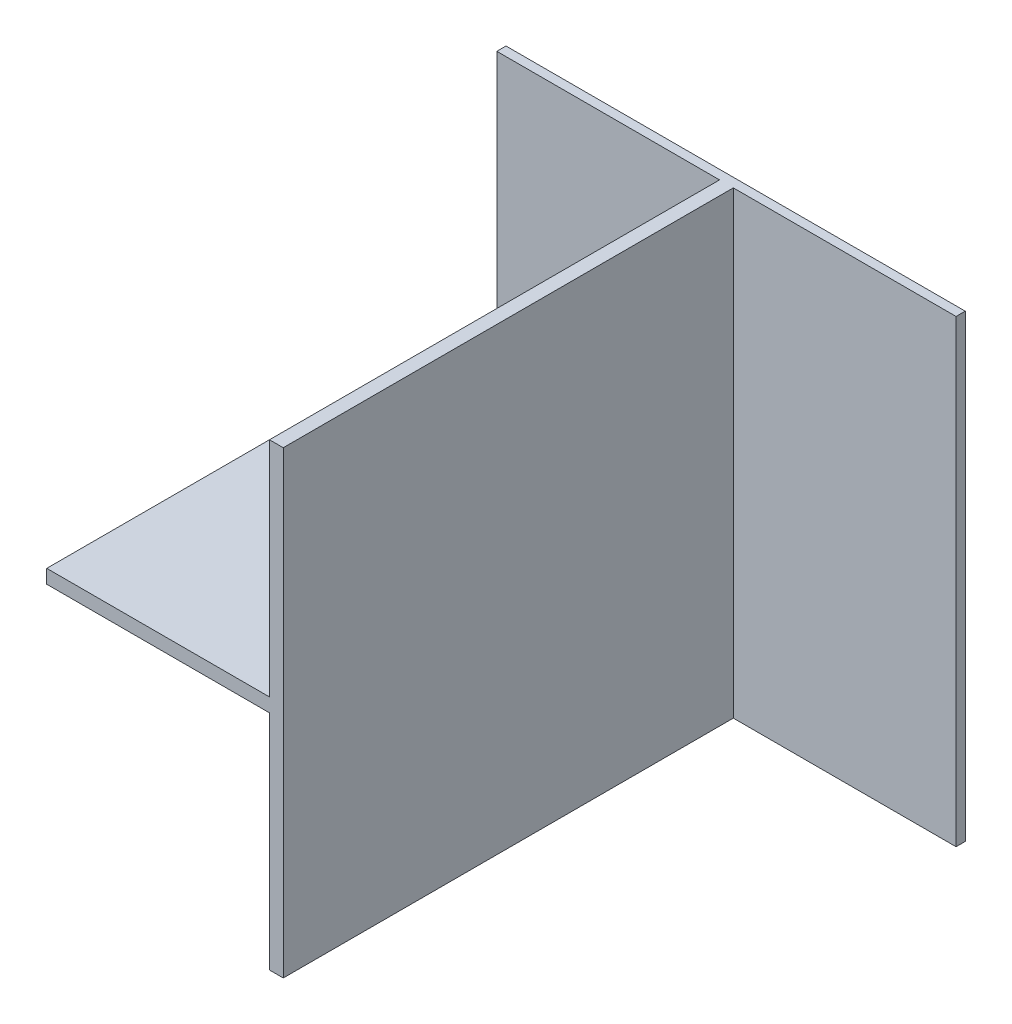
SolidWorks part; units mm, degrees
ref_plane "Płaszczyzna przednia" through (0, 0, 0) normal (0, 0, 1) x (1, 0, 0)
ref_plane "Płaszczyzna górna" through (0, 0, 0) normal (0, 1, 0) x (1, 0, 0)
ref_plane "Płaszczyzna prawa" through (0, 0, 0) normal (1, 0, 0) x (0, 0, -1)
sketch "Szkic1" plane through (0, 0, 0) normal (0, 0, 1) x (1, 0, 0)
  line L0 (0, 0) -> (100, 0)
  line L1 (0, 0) -> (-100, 0)
  line L2 (0, 0) -> (0, 100)
  line L3 (0, 0) -> (0, -100)
  line L4 (0, 100) -> (100, 100)
  line L5 (100, 100) -> (100, 0)
  line L6 (100, -100) -> (0, -100)
  line L7 (100, 0) -> (100, -100)
  line L8 (0, 100) -> (-100, 100)
  line L9 (-100, 100) -> (-100, 0)
  line L10 (-100, -100) -> (-100, 0)
  line L11 (0, -100) -> (-100, -100)
  dimension "D1" = 100
  dimension "D2" = 100
  dimension "D3" = 100
  dimension "D4" = 100
  dimension "D5" = 100
  dimension "D6" = 100
  dimension "D7" = 100
  dimension "D8" = 100
  dimension "D9" = 100
  dimension "D10" = 100
  dimension "D11" = 100
extrude "Dodanie-wyciągnięcie1" add sketch "Szkic1" along normal blind 4 contours L8 L9 L1 L2 | L5 L4 L2 L0 | L7 L0 L3 L6 | L11 L3 L1 L10
sketch "Szkic2" plane through (0, 0, 0) normal (0, 0, 1) x (1, 0, 0)
  line L0 (0, 100) -> (0, -100)
  line L1 (100, 100) -> (-100, 100) construction
  line L2 (100, -100) -> (-100, -100) construction
  line L3 (0, -100) -> (0, 0)
  line L4 (0, 0) -> (-100, 0)
  line L5 (-100, 100) -> (-100, -100) construction
  line L6 (-100, 0) -> (-100, 3)
  line L7 (-100, 0) -> (-100, -3)
  line L8 (0, 100) -> (3, 100)
  line L9 (0, 100) -> (-3, 100)
  line L10 (3, 100) -> (3, -100)
  line L11 (-3, 100) -> (-3, -100)
  line L12 (-100, -3) -> (-3, -3)
  line L13 (-100, 3) -> (-3, 3)
  line L14 (-3, -100) -> (3, -100)
  dimension "D1" = 3
  dimension "D2" = 3
  dimension "D3" = 3
  dimension "D4" = 3
extrude "Dodanie-wyciągnięcie2" add sketch "Szkic2" along normal blind 200 contours L13 L6 L4 L11 | L7 L12 L11 L4 | L0 L14 L10 L8 | L9 L11 L4 L0 | L11 L14 L0 L4
